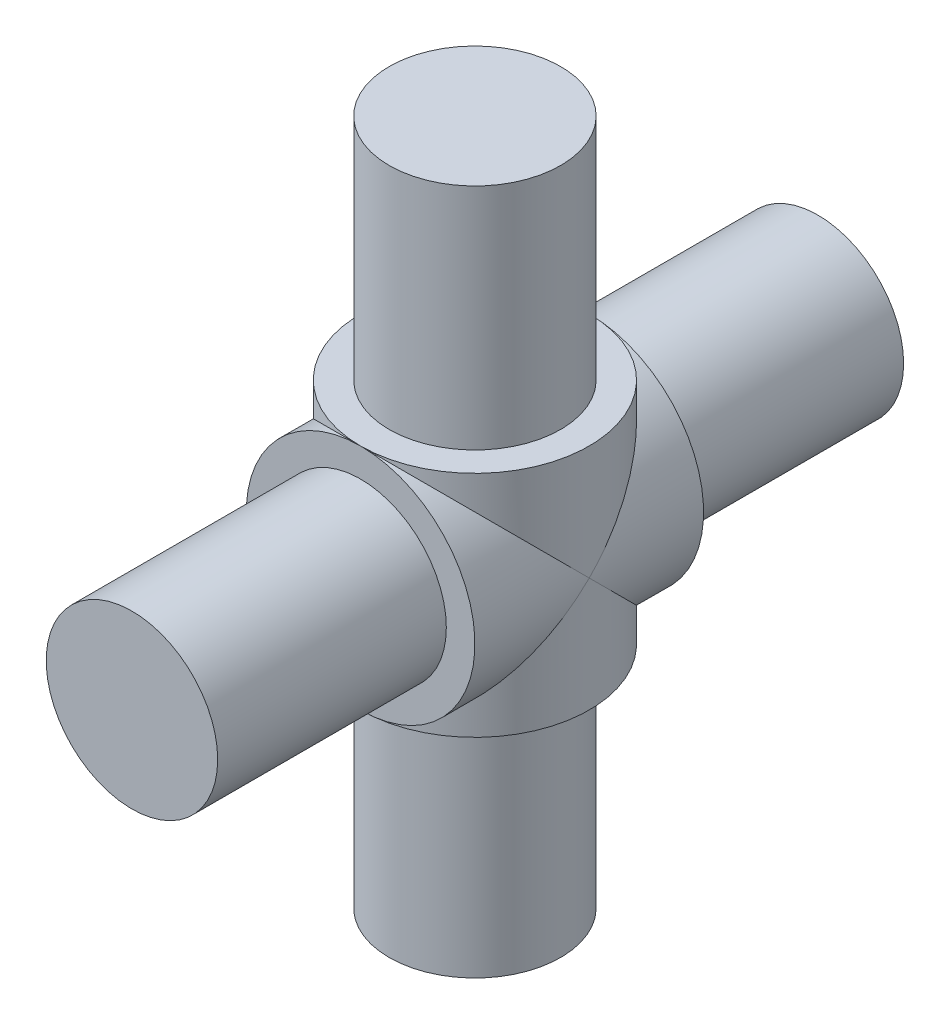
SolidWorks part; units mm, degrees
ref_plane "Front Plane" through (0, 0, 0) normal (0, 0, 1) x (1, 0, 0)
ref_plane "Top Plane" through (0, 0, 0) normal (0, 1, 0) x (1, 0, 0)
ref_plane "Right Plane" through (0, 0, 0) normal (1, 0, 0) x (0, 0, -1)
sketch "Sketch1" plane through (0, 0, 0) normal (0, 0, 1) x (1, 0, 0)
  circle A0 centre (0, 0) radius 10
  dimension "D1" = 20
extrude "Boss-Extrude1" add sketch "Sketch1" along normal mid plane 20
sketch "Sketch2" plane through (0, 0, 0) normal (0, 0, 1) x (1, 0, 0)
  circle A0 centre (0, 0) radius 7.5
  dimension "D1" = 15
extrude "Boss-Extrude2" add sketch "Sketch2" along normal mid plane 60
sketch "Sketch3" plane through (0, 0, 0) normal (0, 1, 0) x (1, 0, 0)
  circle A0 centre (0, 0) radius 10
  dimension "D1" = 20
extrude "Boss-Extrude3" add sketch "Sketch3" along normal mid plane 20
sketch "Sketch4" plane through (0, 0, 0) normal (0, 1, 0) x (1, 0, 0)
  circle A0 centre (0, 0) radius 7.5
  dimension "D1" = 15
extrude "Boss-Extrude4" add sketch "Sketch4" along normal mid plane 60
